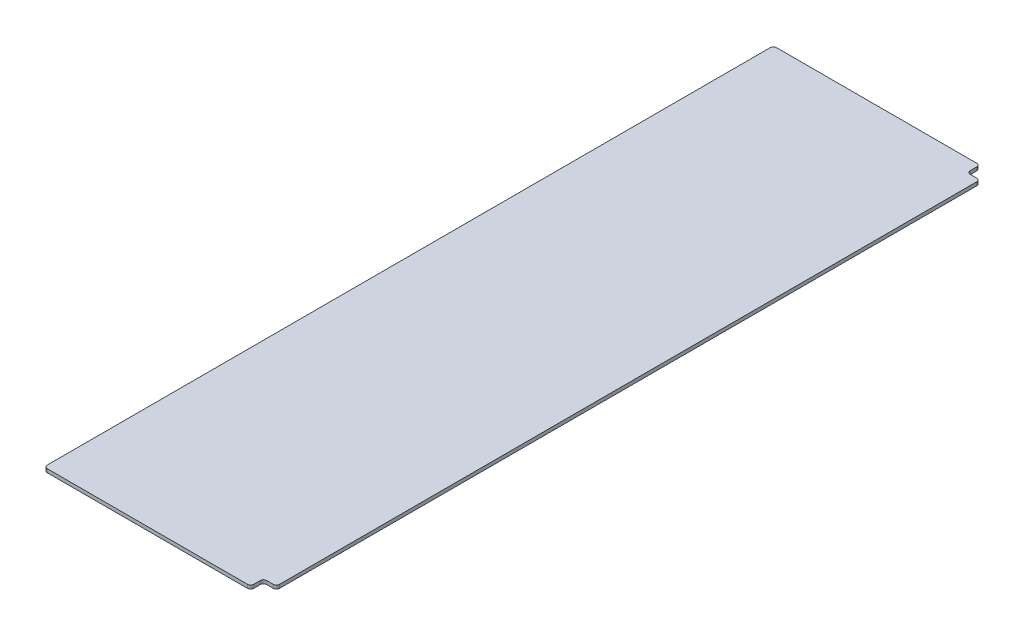
SolidWorks part; units mm, degrees
ref_plane "Front Plane" through (0, 0, 0) normal (0, 0, 1) x (1, 0, 0)
ref_plane "Top Plane" through (0, 0, 0) normal (0, 1, 0) x (1, 0, 0)
ref_plane "Right Plane" through (0, 0, 0) normal (1, 0, 0) x (0, 0, -1)
sketch "Sketch1" plane through (0, 0, 0) normal (0, 1, 0) x (1, 0, 0)
  line L1 (0, 0) -> (190.5, 0)
  line L2 (0, 0) -> (0, 609.6)
  line L3 (0, 609.6) -> (190.5, 609.6)
  line L4 (190.5, 0) -> (190.5, 609.6)
  dimension "D1" = 609.6
  dimension "D2" = 190.5
extrude "Boss-Extrude1" add sketch "Sketch1" along normal blind 2.7781
sketch "Sketch2" plane through (0, 2.7781, 0) normal (0, 1, 0) x (1, 0, 0)
  line L0 (190.5, 0) -> (190.5, 609.6) construction
  line L1 (0, 0) -> (190.5, 0)
  line L2 (0, 0) -> (0, 17.78)
  line L3 (0, 17.78) -> (190.5, 17.78)
  line L4 (190.5, 0) -> (190.5, 17.78)
  line L6 (0, 609.6) -> (190.5, 609.6)
  line L7 (0, 609.6) -> (0, 591.82)
  line L8 (0, 591.82) -> (190.5, 591.82)
  line L9 (190.5, 609.6) -> (190.5, 591.82)
  dimension "D1" = 17.78
  dimension "D2" = 17.78
extrude "Cut-Extrude1" cut sketch "Sketch2" against normal through all
sketch "Sketch3" plane through (0, 2.7781, 0) normal (0, 1, 0) x (1, 0, 0)
  line L0 (190.5, 17.78) -> (0, 17.78) construction
  line L1 (0, 591.82) -> (17.78, 591.82)
  line L2 (0, 591.82) -> (0, 17.78)
  line L3 (0, 17.78) -> (17.78, 17.78)
  line L4 (17.78, 591.82) -> (17.78, 17.78)
  dimension "D1" = 17.78
extrude "Cut-Extrude2" cut sketch "Sketch3" against normal through all
sketch "Sketch4" plane through (0, 2.7781, 0) normal (0, 1, 0) x (1, 0, 0)
  line L16 (190.5, 591.82) -> (180.34, 591.82)
  line L17 (190.5, 591.82) -> (190.5, 581.66)
  line L18 (190.5, 581.66) -> (180.34, 581.66)
  line L19 (180.34, 591.82) -> (180.34, 581.66)
  line L20 (190.5, 17.78) -> (180.34, 17.78)
  line L21 (190.5, 17.78) -> (190.5, 27.94)
  line L22 (190.5, 27.94) -> (180.34, 27.94)
  line L23 (180.34, 17.78) -> (180.34, 27.94)
  dimension "D4" = 10.16
extrude "Cut-Extrude3" cut sketch "Sketch4" against normal through all
fillet "Fillet1" radius 2.54 8 edges at (180.34, 1.3891, -591.82) (190.5, 1.3891, -581.66) (190.5, 1.3891, -27.94) (180.34, 1.3891, -17.78) (180.34, 1.3891, -27.94) (180.34, 1.3891, -581.66) (17.78, 1.3891, -591.82) (17.78, 1.3891, -17.78)
